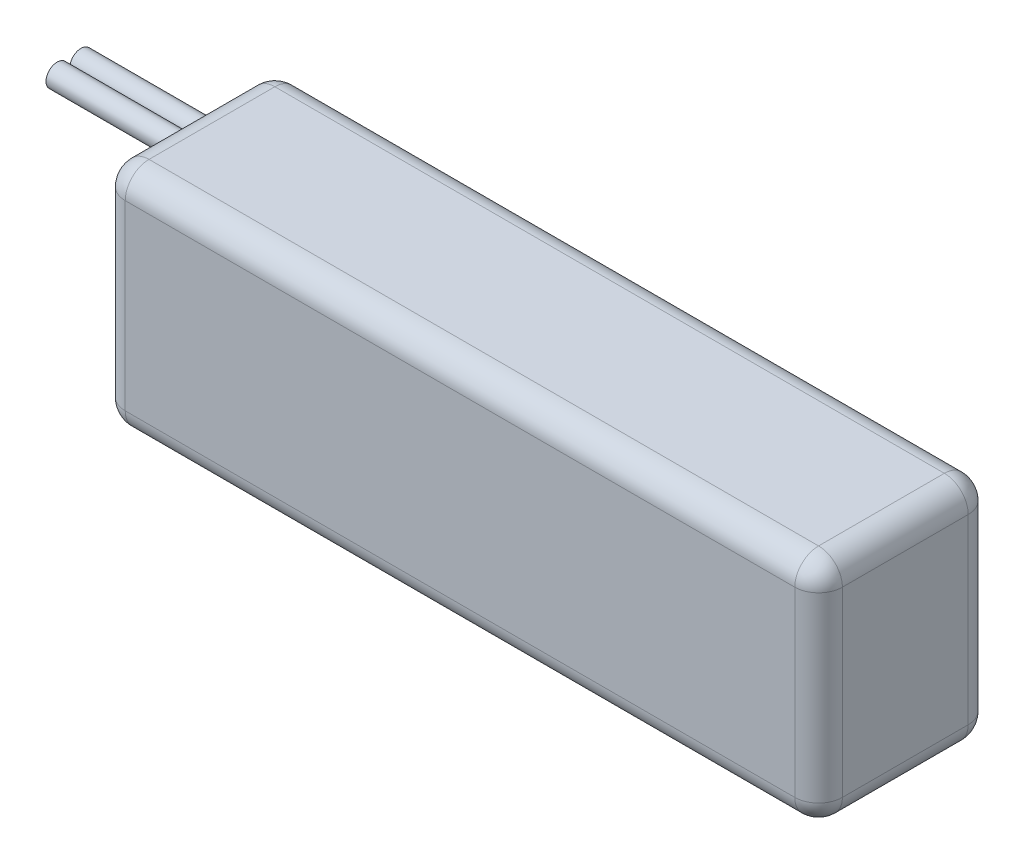
SolidWorks part; units mm, degrees
ref_plane "Front Plane" through (0, 0, 0) normal (0, 0, 1) x (1, 0, 0)
ref_plane "Top Plane" through (0, 0, 0) normal (0, 1, 0) x (1, 0, 0)
ref_plane "Right Plane" through (0, 0, 0) normal (1, 0, 0) x (0, 0, -1)
sketch "Sketch1" plane through (0, 0, 0) normal (0, 1, 0) x (1, 0, 0)
  line L1 (0, 0) -> (153, 0)
  line L2 (0, 0) -> (0, -37)
  line L3 (0, -37) -> (153, -37)
  line L4 (153, 0) -> (153, -37)
  dimension "D1" = 37
  dimension "D2" = 153
extrude "Boss-Extrude1" add sketch "Sketch1" along normal blind 49
fillet "Fillet1" radius 5.08 12 edges at (153, 24.5, 0) (153, 24.5, 37) (153, 0, 18.5) (153, 49, 18.5) (76.5, 49, 0) (76.5, 49, 37) (76.5, 0, 37) (76.5, 0, 0) (0, 0, 18.5) (0, 24.5, 0) (0, 49, 18.5) (0, 24.5, 37)
sketch "Sketch2" plane through (0, 0, 0) normal (-1, 0, 0) x (0, 0, 1)
  line L0 (31.92, 43.92) -> (5.08, 43.92) construction
  line L1 (5.08, 43.92) -> (18.5, 43.92) construction
  line L2 (18.5, 43.92) -> (31.92, 43.92) construction
  circle A0 centre (15.96, 43.92) radius 2.3813
  circle A1 centre (21.04, 43.92) radius 2.3813
  dimension "D1" = 4.7625
  dimension "D2" = 2.54
  dimension "D3" = 2.54
extrude "Boss-Extrude2" add sketch "Sketch2" along normal blind 25.4 and the other way blind 25.4
